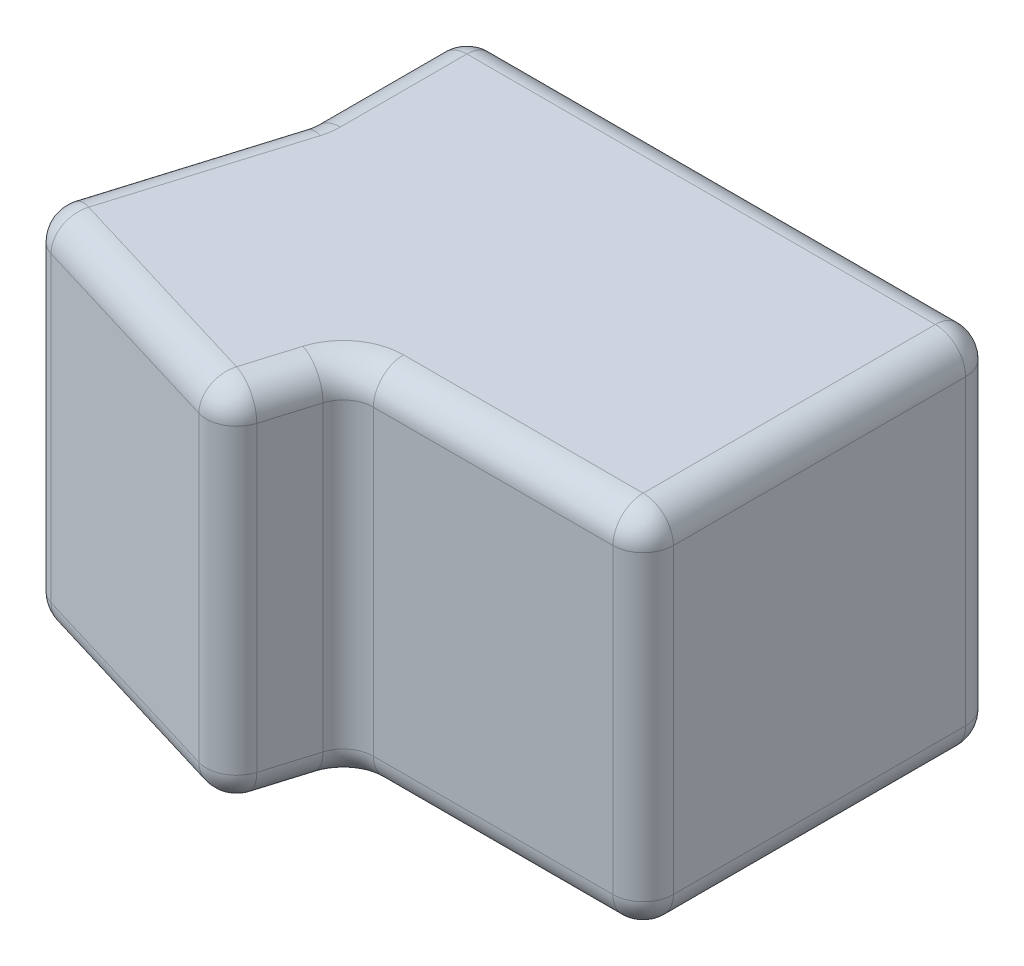
SolidWorks part; units mm, degrees
ref_plane "Front Plane" through (0, 0, 0) normal (0, 0, 1) x (1, 0, 0)
ref_plane "Top Plane" through (0, 0, 0) normal (0, 1, 0) x (1, 0, 0)
ref_plane "Right Plane" through (0, 0, 0) normal (1, 0, 0) x (0, 0, -1)
sketch "Sketch1" plane through (0, 0, 0) normal (0, 1, 0) x (1, 0, 0)
  line L0 (0, 3) -> (0, 32)
  line L1 (-3, 35) -> (-49.5, 35)
  line L2 (-52.5, 32) -> (-52.5, 19.4445)
  line L3 (-52.6289, 18.5746) -> (-57.9718, 0.942)
  line L4 (-55.9706, -2.7991) -> (-34.916, -9.1788)
  line L5 (-31.1749, -7.1777) -> (-29.6454, -2.13)
  line L6 (-26.7743, 0) -> (-3, 0)
  arc A0 (0, 3) -> (-3, 0) centre (-3, 3) cw
  arc A1 (0, 32) -> (-3, 35) centre (-3, 32) ccw
  arc A2 (-49.5, 35) -> (-52.5, 32) centre (-49.5, 32) ccw
  arc A3 (-34.916, -9.1788) -> (-31.1749, -7.1777) centre (-34.046, -6.3078) ccw
  arc A4 (-57.9718, 0.942) -> (-55.9706, -2.7991) centre (-55.1007, 0.072) ccw
  arc A5 (-52.5, 19.4445) -> (-52.6289, 18.5746) centre (-55.5, 19.4445) cw
  arc A6 (-29.6454, -2.13) -> (-26.7743, 0) centre (-26.7743, -3) cw
  point P10 (0, 0)
  point P15 (-52.5, 35)
  point P18 (-32.0449, -10.0488)
  point P21 (-58.8417, -1.9291)
  point P24 (-52.5, 19)
  point P27 (-29, 0)
  dimension "D7" = 3
  dimension "D1" = 52.5
  dimension "D2" = 35
  dimension "D3" = 16
  dimension "D4" = 28
  dimension "D5" = 29
  dimension "D6" = 10.5
extrude "Boss-Extrude1" add sketch "Sketch1" along normal blind 36
fillet "Fillet1" radius 3 28 edges at (-28.5618, 0, 0.5907) (-32.631, 0, 8.9531) (-32.631, 36, 8.9531) (-28.5618, 36, 0.5907) (-0.8787, 0, -0.8787) (-14.8872, 0, 0) (-45.4433, 0, 5.989) (-57.746, 0, 1.343) (-55.3003, 0, -9.7583) (-52.5324, 0, -19.0048) (-52.5, 0, -25.7223) (-51.6213, 0, -34.1213) (-26.25, 0, -35) (-0.8787, 0, -34.1213) (-45.4433, 36, 5.989) (-57.746, 36, 1.343) (-55.3003, 36, -9.7583) (-52.5324, 36, -19.0048) (-52.5, 36, -25.7223) (-51.6213, 36, -34.1213) (-26.25, 36, -35) (-0.8787, 36, -34.1213) (0, 36, -17.5) (-0.8787, 36, -0.8787) (0, 0, -17.5) (-14.8872, 36, 0) (-30.4102, 0, 4.6539) (-30.4102, 36, 4.6539)
hole_wizard "Tap Drill for M3x0.5 Tap1" positions "Sketch2" profile "Sketch3" hole size "M3x0.5" standard "ANSI Metric"
sketch "Sketch2" plane through (0, 0, 0) normal (0, -1, 0) x (-1, 0, 0)
  line L0 (26.7743, 0) -> (3, 0) construction
  line L1 (0, 3) -> (0, 32) construction
  point P0 (7, 25)
  point P2 (45, 25)
  dimension "D1" = 38
  dimension "D2" = 25
  dimension "D3" = 7
sketch "Sketch3" plane through (-7, 0, -25) normal (1, 0, 0) x (0, 0, -1)
  line L0 (0, 0) -> (0, 3.7511)
  line L1 (0, 3.7511) -> (1.25, 3)
  line L2 (1.25, 3) -> (1.25, 0)
  line L5 (1.25, 0) -> (0, 0)
  line L10 (0, 3.7511) -> (-1.25, 3) construction
  line L11 (0, -6.35) -> (0, 107.95) construction
  dimension "Hole Dia." = 2.5
  dimension "Hole Depth" = 3
  dimension "Drill Angle" = 118
